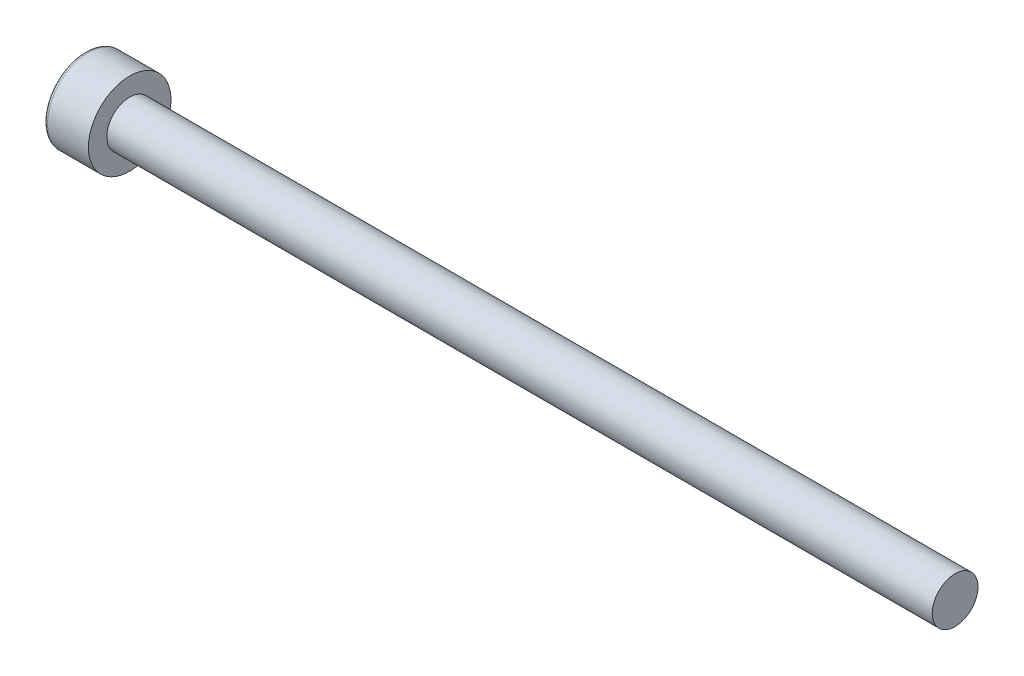
SolidWorks part; units mm, degrees
material "AISI 304"
ref_plane "前视基准面" through (0, 0, 0) normal (0, 0, 1) x (1, 0, 0)
ref_plane "上视基准面" through (0, 0, 0) normal (0, 1, 0) x (1, 0, 0)
ref_plane "右视基准面" through (0, 0, 0) normal (1, 0, 0) x (0, 0, -1)
sketch "草图1" plane through (0, 0, 0) normal (0, 0, 1) x (1, 0, 0)
  line L0 (0, 0) -> (9.1986, 0) construction
  line L1 (0, 0) -> (0, 2.25)
  line L2 (0, 2.25) -> (2.43, 2.25)
  line L3 (2.43, 2.25) -> (2.43, 1.25)
  line L4 (2.43, 1.25) -> (47.43, 1.25)
  line L5 (47.43, 1.25) -> (47.43, 0)
  line L6 (47.43, 0) -> (0, 0)
  dimension "D1" = 2.5
  dimension "长度" = 45
  dimension "D2" = 2.43
  dimension "D3" = 4.5
revolve "旋转1" add sketch "草图1" angle 360 about L0
cosmetic thread "装饰螺纹线1"
sketch "草图2" plane through (0, 0, 0) normal (-1, 0, 0) x (0, 0, 1)
  line L1 (-1.1547, 0) -> (-0.5774, -1)
  line L2 (-0.5774, -1) -> (0.5774, -1)
  line L3 (0.5774, -1) -> (1.1547, 0)
  line L4 (1.1547, 0) -> (0.5774, 1)
  line L5 (0.5774, 1) -> (-0.5774, 1)
  line L6 (-0.5774, 1) -> (-1.1547, 0)
  circle A0 centre (0, 0) radius 1 construction
  dimension "D1" = 2
extrude "切除-拉伸1" cut sketch "草图2" against normal blind 1.1
fillet "圆角1" radius 0.2 1 edges at (0, 0, 2.25)
